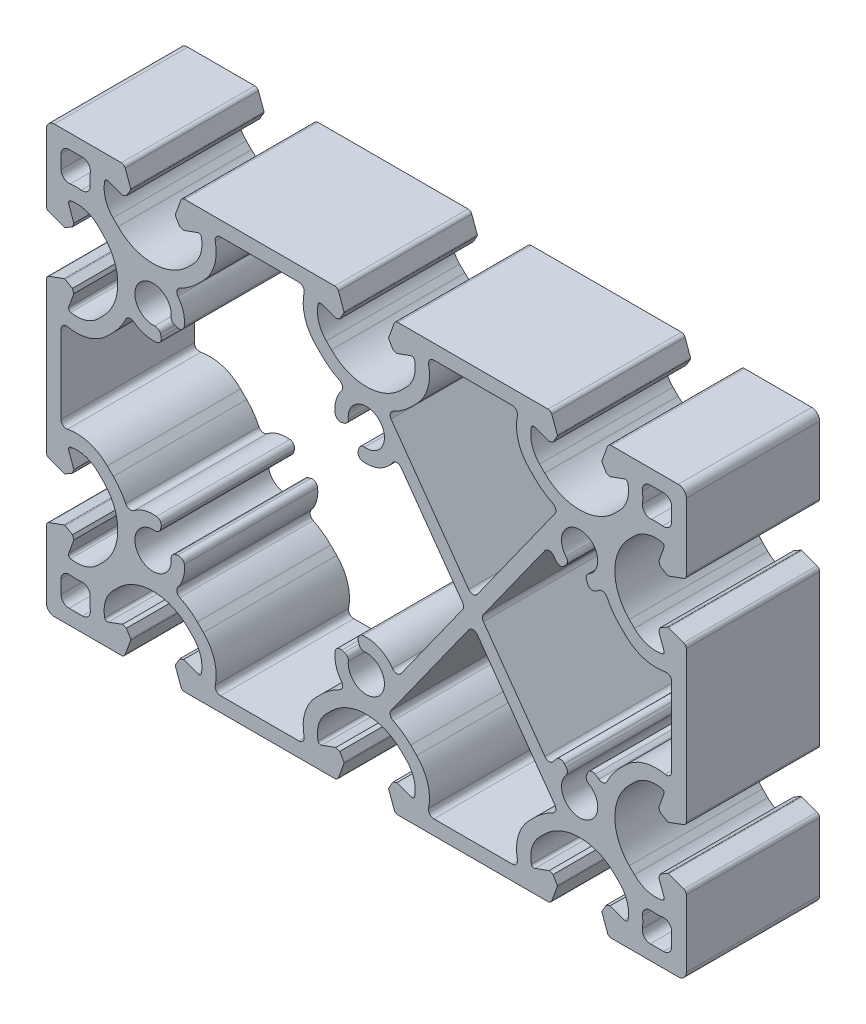
SolidWorks part; units mm, degrees
material "6005-T5"
ref_plane "Front" through (0, 0, 0) normal (0, 0, 1) x (1, 0, 0)
ref_plane "Top" through (0, 0, 0) normal (0, 1, 0) x (1, 0, 0)
ref_plane "Right" through (0, 0, 0) normal (1, 0, 0) x (0, 0, -1)
sketch "Sk Main Extrusion" plane through (0, 0, 0) normal (0, 0, 1) x (1, 0, 0)
  line L0 (-57.25, 35.75) -> (-57.25, 33.2481)
  line L5 (-53.2481, 37.25) -> (-55.75, 37.25)
  line L6 (-38.614, 15.8789) -> (-38.4829, 15.3899)
  line L7 (-47.4415, 11.6915) -> (-48.5773, 10.5557)
  line L8 (-57.25, 7.347) -> (-57.25, -7.347)
  line L9 (-48.5773, -10.5557) -> (-47.4415, -11.6915)
  line L10 (-38.4829, -15.3899) -> (-38.614, -15.8789)
  line L11 (-35.8789, -18.614) -> (-35.3899, -18.4829)
  line L12 (-31.6915, -27.4415) -> (-30.5557, -28.5773)
  line L13 (-27.347, -37.25) -> (-12.653, -37.25)
  line L14 (-9.4443, -28.5773) -> (-8.3085, -27.4415)
  line L15 (-4.6101, -18.4829) -> (-4.1211, -18.614)
  line L16 (-1.386, -15.8789) -> (-1.5171, -15.3899)
  line L17 (6.5268, -16.712) -> (18.0488, -0.5812)
  line L18 (18.0488, 0.5812) -> (6.5268, 16.712)
  line L19 (-1.5171, 15.3899) -> (-1.386, 15.8789)
  line L20 (-4.1211, 18.614) -> (-4.6101, 18.4829)
  line L21 (-8.3085, 27.4415) -> (-9.4443, 28.5773)
  line L22 (-12.653, 37.25) -> (-27.347, 37.25)
  line L23 (-30.5557, 28.5773) -> (-31.6915, 27.4415)
  line L24 (-35.3899, 18.4829) -> (-35.8789, 18.614)
  line L25 (20.8137, 3.2896) -> (35.3545, 23.6466)
  line L26 (31.6915, 27.4415) -> (30.5557, 28.5773)
  line L27 (27.347, 37.25) -> (12.653, 37.25)
  line L28 (9.4443, 28.5773) -> (8.3085, 27.4415)
  line L29 (4.6455, 23.6466) -> (19.1863, 3.2896)
  line L30 (-57.25, -33.2481) -> (-57.25, -35.75)
  line L31 (-55.75, -37.25) -> (-53.2481, -37.25)
  line L32 (19.1863, -3.2896) -> (4.6455, -23.6466)
  line L33 (8.3085, -27.4415) -> (9.4443, -28.5773)
  line L34 (12.653, -37.25) -> (27.347, -37.25)
  line L35 (30.5557, -28.5773) -> (31.6915, -27.4415)
  line L36 (35.3545, -23.6466) -> (20.8137, -3.2896)
  line L37 (41.2964, -15.8498) -> (41.4773, -15.377)
  line L38 (47.4415, -11.6915) -> (48.5773, -10.5557)
  line L39 (57.25, -7.347) -> (57.25, 7.347)
  line L40 (48.5773, 10.5557) -> (47.4415, 11.6915)
  line L41 (41.4773, 15.377) -> (41.2964, 15.8498)
  line L42 (37.4767, 16.4592) -> (37.1577, 16.0661)
  line L43 (33.4732, 16.712) -> (21.9512, 0.5812)
  line L44 (21.9512, -0.5812) -> (33.4732, -16.712)
  line L45 (37.1577, -16.0661) -> (37.4767, -16.4592)
  line L46 (53.2481, -37.25) -> (55.75, -37.25)
  line L47 (57.25, -35.75) -> (57.25, -33.2481)
  line L48 (57.25, 33.2481) -> (57.25, 35.75)
  line L49 (55.75, 37.25) -> (53.2481, 37.25)
  line L50 (-35.8099, -36.6712) -> (-34.7779, -39.5065)
  line L51 (-34.0732, -40) -> (-5.9268, -40)
  line L52 (-5.2221, -39.5065) -> (-4.1901, -36.6712)
  line L53 (-4.2085, -36.4607) -> (-4.9876, -35.1113)
  line L54 (-4.9876, -35.1113) -> (-5.7185, -34.8453)
  line L55 (-5.7185, -34.8453) -> (-8.3962, -35.8198)
  line L56 (-7.5042, -30.2727) -> (-6.5407, -29.3093)
  line L57 (6.5407, -29.3093) -> (7.5042, -30.2727)
  line L58 (8.3962, -35.8198) -> (5.7185, -34.8453)
  line L59 (5.7185, -34.8453) -> (4.9876, -35.1113)
  line L60 (4.9876, -35.1113) -> (4.2085, -36.4607)
  line L61 (4.1901, -36.6712) -> (5.2221, -39.5065)
  line L62 (5.9268, -40) -> (34.0732, -40)
  line L63 (34.7779, -39.5065) -> (35.8099, -36.6712)
  line L64 (35.7915, -36.4607) -> (35.0124, -35.1113)
  line L65 (35.0124, -35.1113) -> (34.2815, -34.8453)
  line L66 (34.2815, -34.8453) -> (31.6038, -35.8198)
  line L67 (32.4958, -30.2727) -> (33.4593, -29.3093)
  line L68 (46.5407, -29.3093) -> (47.5042, -30.2727)
  line L69 (48.3962, -35.8198) -> (45.7185, -34.8453)
  line L70 (45.7185, -34.8453) -> (44.9876, -35.1113)
  line L71 (44.9876, -35.1113) -> (44.2085, -36.4607)
  line L72 (44.1901, -36.6712) -> (45.2221, -39.5065)
  line L73 (45.9268, -40) -> (58.5, -40)
  line L74 (60, -38.5) -> (60, -25.9268)
  line L75 (59.5065, -25.2221) -> (56.6712, -24.1901)
  line L76 (56.4607, -24.2085) -> (55.1113, -24.9876)
  line L77 (55.1113, -24.9876) -> (54.8453, -25.7185)
  line L78 (54.8453, -25.7185) -> (55.8198, -28.3962)
  line L79 (50.2727, -27.5042) -> (49.3093, -26.5407)
  line L80 (49.3093, -13.4593) -> (50.2727, -12.4958)
  line L81 (55.8198, -11.6038) -> (54.8453, -14.2815)
  line L82 (54.8453, -14.2815) -> (55.1113, -15.0124)
  line L83 (55.1113, -15.0124) -> (56.4607, -15.7915)
  line L84 (56.6712, -15.8099) -> (59.5065, -14.7779)
  line L85 (60, -14.0732) -> (60, 14.0732)
  line L86 (59.5065, 14.7779) -> (56.6712, 15.8099)
  line L87 (56.4607, 15.7915) -> (55.1113, 15.0124)
  line L88 (55.1113, 15.0124) -> (54.8453, 14.2815)
  line L89 (54.8453, 14.2815) -> (55.8198, 11.6038)
  line L90 (50.2727, 12.4958) -> (49.3093, 13.4593)
  line L91 (49.3093, 26.5407) -> (50.2727, 27.5042)
  line L92 (55.8198, 28.3962) -> (54.8453, 25.7185)
  line L93 (54.8453, 25.7185) -> (55.1113, 24.9876)
  line L94 (55.1113, 24.9876) -> (56.4607, 24.2085)
  line L95 (56.6712, 24.1901) -> (59.5065, 25.2221)
  line L96 (60, 25.9268) -> (60, 38.5)
  line L97 (58.5, 40) -> (45.9268, 40)
  line L98 (45.2221, 39.5065) -> (44.1901, 36.6712)
  line L99 (44.2085, 36.4607) -> (44.9876, 35.1113)
  line L100 (44.9876, 35.1113) -> (45.7185, 34.8453)
  line L101 (45.7185, 34.8453) -> (48.3962, 35.8198)
  line L102 (47.5042, 30.2727) -> (46.5407, 29.3093)
  line L103 (33.4593, 29.3093) -> (32.4958, 30.2727)
  line L104 (31.6038, 35.8198) -> (34.2815, 34.8453)
  line L105 (34.2815, 34.8453) -> (35.0124, 35.1113)
  line L106 (35.0124, 35.1113) -> (35.7915, 36.4607)
  line L107 (35.8099, 36.6712) -> (34.7779, 39.5065)
  line L108 (34.0732, 40) -> (5.9268, 40)
  line L109 (5.2221, 39.5065) -> (4.1901, 36.6712)
  line L110 (4.2085, 36.4607) -> (4.9876, 35.1113)
  line L111 (4.9876, 35.1113) -> (5.7185, 34.8453)
  line L112 (5.7185, 34.8453) -> (8.3962, 35.8198)
  line L113 (7.5042, 30.2727) -> (6.5407, 29.3093)
  line L114 (-6.5407, 29.3093) -> (-7.5042, 30.2727)
  line L115 (-8.3962, 35.8198) -> (-5.7185, 34.8453)
  line L116 (-5.7185, 34.8453) -> (-4.9876, 35.1113)
  line L117 (-4.9876, 35.1113) -> (-4.2085, 36.4607)
  line L118 (-4.1901, 36.6712) -> (-5.2221, 39.5065)
  line L119 (-5.9268, 40) -> (-34.0732, 40)
  line L120 (-34.7779, 39.5065) -> (-35.8099, 36.6712)
  line L121 (-35.7915, 36.4607) -> (-35.0124, 35.1113)
  line L122 (-35.0124, 35.1113) -> (-34.2815, 34.8453)
  line L123 (-34.2815, 34.8453) -> (-31.6038, 35.8198)
  line L124 (-32.4958, 30.2727) -> (-33.4593, 29.3093)
  line L125 (-46.5407, 29.3093) -> (-47.5042, 30.2727)
  line L126 (-48.3962, 35.8198) -> (-45.7185, 34.8453)
  line L127 (-45.7185, 34.8453) -> (-44.9876, 35.1113)
  line L128 (-44.9876, 35.1113) -> (-44.2085, 36.4607)
  line L129 (-44.1901, 36.6712) -> (-45.2221, 39.5065)
  line L130 (-45.9268, 40) -> (-58.5, 40)
  line L131 (-60, 38.5) -> (-60, 25.9268)
  line L132 (-59.5065, 25.2221) -> (-56.6712, 24.1901)
  line L133 (-56.4607, 24.2085) -> (-55.1113, 24.9876)
  line L134 (-55.1113, 24.9876) -> (-54.8453, 25.7185)
  line L135 (-54.8453, 25.7185) -> (-55.8198, 28.3962)
  line L136 (-50.2727, 27.5042) -> (-49.3093, 26.5407)
  line L137 (-49.3093, 13.4593) -> (-50.2727, 12.4958)
  line L138 (-55.8198, 11.6038) -> (-54.8453, 14.2815)
  line L139 (-54.8453, 14.2815) -> (-55.1113, 15.0124)
  line L140 (-55.1113, 15.0124) -> (-56.4607, 15.7915)
  line L141 (-56.6712, 15.8099) -> (-59.5065, 14.7779)
  line L142 (-60, 14.0732) -> (-60, -14.0732)
  line L143 (-59.5065, -14.7779) -> (-56.6712, -15.8099)
  line L144 (-56.4607, -15.7915) -> (-55.1113, -15.0124)
  line L145 (-55.1113, -15.0124) -> (-54.8453, -14.2815)
  line L146 (-54.8453, -14.2815) -> (-55.8198, -11.6038)
  line L147 (-50.2727, -12.4958) -> (-49.3093, -13.4593)
  line L148 (-49.3093, -26.5407) -> (-50.2727, -27.5042)
  line L149 (-55.8198, -28.3962) -> (-54.8453, -25.7185)
  line L150 (-54.8453, -25.7185) -> (-55.1113, -24.9876)
  line L151 (-55.1113, -24.9876) -> (-56.4607, -24.2085)
  line L152 (-56.6712, -24.1901) -> (-59.5065, -25.2221)
  line L153 (-60, -25.9268) -> (-60, -38.5)
  line L154 (-58.5, -40) -> (-45.9268, -40)
  line L155 (-45.2221, -39.5065) -> (-44.1901, -36.6712)
  line L156 (-44.2085, -36.4607) -> (-44.9876, -35.1113)
  line L157 (-44.9876, -35.1113) -> (-45.7185, -34.8453)
  line L158 (-45.7185, -34.8453) -> (-48.3962, -35.8198)
  line L159 (-47.5042, -30.2727) -> (-46.5407, -29.3093)
  line L160 (-33.4593, -29.3093) -> (-32.4958, -30.2727)
  line L161 (-31.6038, -35.8198) -> (-34.2815, -34.8453)
  line L162 (-34.2815, -34.8453) -> (-35.0124, -35.1113)
  line L163 (-35.0124, -35.1113) -> (-35.7915, -36.4607)
  line L164 (-57.25, 0) -> (57.25, 0) construction
  line L165 (0, 0) -> (0, 40) construction
  arc A0 (-55.75, 37.25) -> (-57.25, 35.75) centre (-55.75, 35.75) ccw
  arc A1 (-57.25, 33.2481) -> (-55.5375, 31.7633) centre (-55.75, 33.2481) ccw
  arc A2 (-53.4532, 31.794) -> (-55.5375, 31.7633) centre (-54.3755, 23.646) ccw
  arc A3 (-53.4532, 31.794) -> (-51.794, 33.4532) centre (-53.2844, 33.2844) ccw
  arc A4 (-51.7633, 35.5375) -> (-51.794, 33.4532) centre (-43.646, 34.3755) ccw
  arc A5 (-51.7633, 35.5375) -> (-53.2481, 37.25) centre (-53.2481, 35.75) ccw
  arc A6 (-38.614, 15.8789) -> (-39.6754, 16.6155) centre (-39.5799, 15.6201) ccw
  arc A7 (-39.3364, 14.1374) -> (-38.4829, 15.3899) centre (-39.4489, 15.1311) ccw
  arc A8 (-43.6133, 15.3359) -> (-39.3364, 14.1374) centre (-40, 20) ccw
  arc A9 (-43.6133, 15.3359) -> (-45.1296, 14.9732) centre (-44.2257, 14.5453) ccw
  arc A10 (-47.4415, 11.6915) -> (-45.1296, 14.9732) centre (-55.75, 20) ccw
  arc A11 (-56.0463, 8.326) -> (-48.5773, 10.5557) centre (-54.3755, 16.354) ccw
  arc A12 (-56.0463, 8.326) -> (-57.25, 7.347) centre (-56.25, 7.347) ccw
  arc A13 (-57.25, -7.347) -> (-56.0463, -8.326) centre (-56.25, -7.347) ccw
  arc A14 (-48.5773, -10.5557) -> (-56.0463, -8.326) centre (-54.3755, -16.354) ccw
  arc A15 (-45.1296, -14.9732) -> (-47.4415, -11.6915) centre (-55.75, -20) ccw
  arc A16 (-45.1296, -14.9732) -> (-43.6133, -15.3359) centre (-44.2257, -14.5453) ccw
  arc A17 (-39.3364, -14.1374) -> (-43.6133, -15.3359) centre (-40, -20) ccw
  arc A18 (-38.4829, -15.3899) -> (-39.3364, -14.1374) centre (-39.4489, -15.1311) ccw
  arc A19 (-39.6754, -16.6155) -> (-38.614, -15.8789) centre (-39.5799, -15.6201) ccw
  arc A20 (-39.6754, -16.6155) -> (-36.6155, -19.6754) centre (-40, -20) ccw
  arc A21 (-35.8789, -18.614) -> (-36.6155, -19.6754) centre (-35.6201, -19.5799) ccw
  arc A22 (-34.1374, -19.3364) -> (-35.3899, -18.4829) centre (-35.1311, -19.4489) ccw
  arc A23 (-35.3359, -23.6133) -> (-34.1374, -19.3364) centre (-40, -20) ccw
  arc A24 (-35.3359, -23.6133) -> (-34.9732, -25.1296) centre (-34.5453, -24.2257) ccw
  arc A25 (-31.6915, -27.4415) -> (-34.9732, -25.1296) centre (-40, -35.75) ccw
  arc A26 (-28.326, -36.0463) -> (-30.5557, -28.5773) centre (-36.354, -34.3755) ccw
  arc A27 (-28.326, -36.0463) -> (-27.347, -37.25) centre (-27.347, -36.25) ccw
  arc A28 (-12.653, -37.25) -> (-11.674, -36.0463) centre (-12.653, -36.25) ccw
  arc A29 (-9.4443, -28.5773) -> (-11.674, -36.0463) centre (-3.646, -34.3755) ccw
  arc A30 (-5.0268, -25.1296) -> (-8.3085, -27.4415) centre (0, -35.75) ccw
  arc A31 (-5.0268, -25.1296) -> (-4.6641, -23.6133) centre (-5.4547, -24.2257) ccw
  arc A32 (-5.8626, -19.3364) -> (-4.6641, -23.6133) centre (0, -20) ccw
  arc A33 (-34.7779, -39.5065) -> (-34.0732, -40) centre (-34.0732, -39.25) ccw
  arc A34 (-5.9268, -40) -> (-5.2221, -39.5065) centre (-5.9268, -39.25) ccw
  arc A35 (-4.1901, -36.6712) -> (-4.2085, -36.4607) centre (-4.425, -36.5857) ccw
  arc A36 (-9.057, -35.4507) -> (-8.3962, -35.8198) centre (-8.5672, -35.35) ccw
  arc A37 (-7.5042, -30.2727) -> (-9.057, -35.4507) centre (-3.4737, -34.3032) ccw
  arc A38 (6.5407, -29.3093) -> (-6.5407, -29.3093) centre (0, -35.85) ccw
  arc A39 (9.057, -35.4507) -> (7.5042, -30.2727) centre (3.4737, -34.3032) ccw
  arc A40 (8.3962, -35.8198) -> (9.057, -35.4507) centre (8.5672, -35.35) ccw
  arc A41 (4.2085, -36.4607) -> (4.1901, -36.6712) centre (4.425, -36.5857) ccw
  arc A42 (5.2221, -39.5065) -> (5.9268, -40) centre (5.9268, -39.25) ccw
  arc A43 (34.0732, -40) -> (34.7779, -39.5065) centre (34.0732, -39.25) ccw
  arc A44 (35.8099, -36.6712) -> (35.7915, -36.4607) centre (35.575, -36.5857) ccw
  arc A45 (30.943, -35.4507) -> (31.6038, -35.8198) centre (31.4328, -35.35) ccw
  arc A46 (32.4958, -30.2727) -> (30.943, -35.4507) centre (36.5263, -34.3032) ccw
  arc A47 (46.5407, -29.3093) -> (33.4593, -29.3093) centre (40, -35.85) ccw
  arc A48 (49.057, -35.4507) -> (47.5042, -30.2727) centre (43.4737, -34.3032) ccw
  arc A49 (48.3962, -35.8198) -> (49.057, -35.4507) centre (48.5672, -35.35) ccw
  arc A50 (44.2085, -36.4607) -> (44.1901, -36.6712) centre (44.425, -36.5857) ccw
  arc A51 (45.2221, -39.5065) -> (45.9268, -40) centre (45.9268, -39.25) ccw
  arc A52 (58.5, -40) -> (60, -38.5) centre (58.5, -38.5) ccw
  arc A53 (60, -25.9268) -> (59.5065, -25.2221) centre (59.25, -25.9268) ccw
  arc A54 (56.6712, -24.1901) -> (56.4607, -24.2085) centre (56.5857, -24.425) ccw
  arc A55 (55.4507, -29.057) -> (55.8198, -28.3962) centre (55.35, -28.5672) ccw
  arc A56 (50.2727, -27.5042) -> (55.4507, -29.057) centre (54.3032, -23.4737) ccw
  arc A57 (49.3093, -13.4593) -> (49.3093, -26.5407) centre (55.85, -20) ccw
  arc A58 (55.4507, -10.943) -> (50.2727, -12.4958) centre (54.3032, -16.5263) ccw
  arc A59 (55.8198, -11.6038) -> (55.4507, -10.943) centre (55.35, -11.4328) ccw
  arc A60 (56.4607, -15.7915) -> (56.6712, -15.8099) centre (56.5857, -15.575) ccw
  arc A61 (59.5065, -14.7779) -> (60, -14.0732) centre (59.25, -14.0732) ccw
  arc A62 (60, 14.0732) -> (59.5065, 14.7779) centre (59.25, 14.0732) ccw
  arc A63 (56.6712, 15.8099) -> (56.4607, 15.7915) centre (56.5857, 15.575) ccw
  arc A64 (55.4507, 10.943) -> (55.8198, 11.6038) centre (55.35, 11.4328) ccw
  arc A65 (50.2727, 12.4958) -> (55.4507, 10.943) centre (54.3032, 16.5263) ccw
  arc A66 (49.3093, 26.5407) -> (49.3093, 13.4593) centre (55.85, 20) ccw
  arc A67 (55.4507, 29.057) -> (50.2727, 27.5042) centre (54.3032, 23.4737) ccw
  arc A68 (55.8198, 28.3962) -> (55.4507, 29.057) centre (55.35, 28.5672) ccw
  arc A69 (56.4607, 24.2085) -> (56.6712, 24.1901) centre (56.5857, 24.425) ccw
  arc A70 (59.5065, 25.2221) -> (60, 25.9268) centre (59.25, 25.9268) ccw
  arc A71 (60, 38.5) -> (58.5, 40) centre (58.5, 38.5) ccw
  arc A72 (45.9268, 40) -> (45.2221, 39.5065) centre (45.9268, 39.25) ccw
  arc A73 (44.1901, 36.6712) -> (44.2085, 36.4607) centre (44.425, 36.5857) ccw
  arc A74 (49.057, 35.4507) -> (48.3962, 35.8198) centre (48.5672, 35.35) ccw
  arc A75 (47.5042, 30.2727) -> (49.057, 35.4507) centre (43.4737, 34.3032) ccw
  arc A76 (33.4593, 29.3093) -> (46.5407, 29.3093) centre (40, 35.85) ccw
  arc A77 (30.943, 35.4507) -> (32.4958, 30.2727) centre (36.5263, 34.3032) ccw
  arc A78 (31.6038, 35.8198) -> (30.943, 35.4507) centre (31.4328, 35.35) ccw
  arc A79 (35.7915, 36.4607) -> (35.8099, 36.6712) centre (35.575, 36.5857) ccw
  arc A80 (34.7779, 39.5065) -> (34.0732, 40) centre (34.0732, 39.25) ccw
  arc A81 (5.9268, 40) -> (5.2221, 39.5065) centre (5.9268, 39.25) ccw
  arc A82 (4.1901, 36.6712) -> (4.2085, 36.4607) centre (4.425, 36.5857) ccw
  arc A83 (9.057, 35.4507) -> (8.3962, 35.8198) centre (8.5672, 35.35) ccw
  arc A84 (7.5042, 30.2727) -> (9.057, 35.4507) centre (3.4737, 34.3032) ccw
  arc A85 (-6.5407, 29.3093) -> (6.5407, 29.3093) centre (0, 35.85) ccw
  arc A86 (-9.057, 35.4507) -> (-7.5042, 30.2727) centre (-3.4737, 34.3032) ccw
  arc A87 (-8.3962, 35.8198) -> (-9.057, 35.4507) centre (-8.5672, 35.35) ccw
  arc A88 (-4.2085, 36.4607) -> (-4.1901, 36.6712) centre (-4.425, 36.5857) ccw
  arc A89 (-5.2221, 39.5065) -> (-5.9268, 40) centre (-5.9268, 39.25) ccw
  arc A90 (-34.0732, 40) -> (-34.7779, 39.5065) centre (-34.0732, 39.25) ccw
  arc A91 (-35.8099, 36.6712) -> (-35.7915, 36.4607) centre (-35.575, 36.5857) ccw
  arc A92 (-30.943, 35.4507) -> (-31.6038, 35.8198) centre (-31.4328, 35.35) ccw
  arc A93 (-32.4958, 30.2727) -> (-30.943, 35.4507) centre (-36.5263, 34.3032) ccw
  arc A94 (-46.5407, 29.3093) -> (-33.4593, 29.3093) centre (-40, 35.85) ccw
  arc A95 (-49.057, 35.4507) -> (-47.5042, 30.2727) centre (-43.4737, 34.3032) ccw
  arc A96 (-48.3962, 35.8198) -> (-49.057, 35.4507) centre (-48.5672, 35.35) ccw
  arc A97 (-44.2085, 36.4607) -> (-44.1901, 36.6712) centre (-44.425, 36.5857) ccw
  arc A98 (-45.2221, 39.5065) -> (-45.9268, 40) centre (-45.9268, 39.25) ccw
  arc A99 (-58.5, 40) -> (-60, 38.5) centre (-58.5, 38.5) ccw
  arc A100 (-60, 25.9268) -> (-59.5065, 25.2221) centre (-59.25, 25.9268) ccw
  arc A101 (-56.6712, 24.1901) -> (-56.4607, 24.2085) centre (-56.5857, 24.425) ccw
  arc A102 (-55.4507, 29.057) -> (-55.8198, 28.3962) centre (-55.35, 28.5672) ccw
  arc A103 (-50.2727, 27.5042) -> (-55.4507, 29.057) centre (-54.3032, 23.4737) ccw
  arc A104 (-49.3093, 13.4593) -> (-49.3093, 26.5407) centre (-55.85, 20) ccw
  arc A105 (-55.4507, 10.943) -> (-50.2727, 12.4958) centre (-54.3032, 16.5263) ccw
  arc A106 (-55.8198, 11.6038) -> (-55.4507, 10.943) centre (-55.35, 11.4328) ccw
  arc A107 (-56.4607, 15.7915) -> (-56.6712, 15.8099) centre (-56.5857, 15.575) ccw
  arc A108 (-59.5065, 14.7779) -> (-60, 14.0732) centre (-59.25, 14.0732) ccw
  arc A109 (-60, -14.0732) -> (-59.5065, -14.7779) centre (-59.25, -14.0732) ccw
  arc A110 (-56.6712, -15.8099) -> (-56.4607, -15.7915) centre (-56.5857, -15.575) ccw
  arc A111 (-55.4507, -10.943) -> (-55.8198, -11.6038) centre (-55.35, -11.4328) ccw
  arc A112 (-50.2727, -12.4958) -> (-55.4507, -10.943) centre (-54.3032, -16.5263) ccw
  arc A113 (-49.3093, -26.5407) -> (-49.3093, -13.4593) centre (-55.85, -20) ccw
  arc A114 (-55.4507, -29.057) -> (-50.2727, -27.5042) centre (-54.3032, -23.4737) ccw
  arc A115 (-55.8198, -28.3962) -> (-55.4507, -29.057) centre (-55.35, -28.5672) ccw
  arc A116 (-56.4607, -24.2085) -> (-56.6712, -24.1901) centre (-56.5857, -24.425) ccw
  arc A117 (-59.5065, -25.2221) -> (-60, -25.9268) centre (-59.25, -25.9268) ccw
  arc A118 (-60, -38.5) -> (-58.5, -40) centre (-58.5, -38.5) ccw
  arc A119 (-45.9268, -40) -> (-45.2221, -39.5065) centre (-45.9268, -39.25) ccw
  arc A120 (-44.1901, -36.6712) -> (-44.2085, -36.4607) centre (-44.425, -36.5857) ccw
  arc A121 (-49.057, -35.4507) -> (-48.3962, -35.8198) centre (-48.5672, -35.35) ccw
  arc A122 (-47.5042, -30.2727) -> (-49.057, -35.4507) centre (-43.4737, -34.3032) ccw
  arc A123 (-33.4593, -29.3093) -> (-46.5407, -29.3093) centre (-40, -35.85) ccw
  arc A124 (-30.943, -35.4507) -> (-32.4958, -30.2727) centre (-36.5263, -34.3032) ccw
  arc A125 (-31.6038, -35.8198) -> (-30.943, -35.4507) centre (-31.4328, -35.35) ccw
  arc A126 (-35.7915, -36.4607) -> (-35.8099, -36.6712) centre (-35.575, -36.5857) ccw
  arc A127 (-4.6101, -18.4829) -> (-5.8626, -19.3364) centre (-4.8689, -19.4489) ccw
  arc A128 (-3.3845, -19.6754) -> (-4.1211, -18.614) centre (-4.3799, -19.5799) ccw
  arc A129 (-3.3845, -19.6754) -> (-0.3246, -16.6155) centre (0, -20) ccw
  arc A130 (-1.386, -15.8789) -> (-0.3246, -16.6155) centre (-0.4201, -15.6201) ccw
  arc A131 (-0.6636, -14.1374) -> (-1.5171, -15.3899) centre (-0.5511, -15.1311) ccw
  arc A132 (4.8851, -16.6916) -> (-0.6636, -14.1374) centre (0, -20) ccw
  arc A133 (4.8851, -16.6916) -> (6.5268, -16.712) centre (5.7131, -16.1308) ccw
  arc A134 (18.0488, -0.5812) -> (18.0488, 0.5812) centre (17.2351, 0) ccw
  arc A135 (6.5268, 16.712) -> (4.8851, 16.6916) centre (5.7131, 16.1308) ccw
  arc A136 (-0.6636, 14.1374) -> (4.8851, 16.6916) centre (0, 20) ccw
  arc A137 (-1.5171, 15.3899) -> (-0.6636, 14.1374) centre (-0.5511, 15.1311) ccw
  arc A138 (-0.3246, 16.6155) -> (-1.386, 15.8789) centre (-0.4201, 15.6201) ccw
  arc A139 (-0.3246, 16.6155) -> (-3.3845, 19.6754) centre (0, 20) ccw
  arc A140 (-4.1211, 18.614) -> (-3.3845, 19.6754) centre (-4.3799, 19.5799) ccw
  arc A141 (-5.8626, 19.3364) -> (-4.6101, 18.4829) centre (-4.8689, 19.4489) ccw
  arc A142 (-4.6641, 23.6133) -> (-5.8626, 19.3364) centre (0, 20) ccw
  arc A143 (-4.6641, 23.6133) -> (-5.0268, 25.1296) centre (-5.4547, 24.2257) ccw
  arc A144 (-8.3085, 27.4415) -> (-5.0268, 25.1296) centre (0, 35.75) ccw
  arc A145 (-11.674, 36.0463) -> (-9.4443, 28.5773) centre (-3.646, 34.3755) ccw
  arc A146 (-11.674, 36.0463) -> (-12.653, 37.25) centre (-12.653, 36.25) ccw
  arc A147 (-27.347, 37.25) -> (-28.326, 36.0463) centre (-27.347, 36.25) ccw
  arc A148 (-30.5557, 28.5773) -> (-28.326, 36.0463) centre (-36.354, 34.3755) ccw
  arc A149 (-34.9732, 25.1296) -> (-31.6915, 27.4415) centre (-40, 35.75) ccw
  arc A150 (-34.9732, 25.1296) -> (-35.3359, 23.6133) centre (-34.5453, 24.2257) ccw
  arc A151 (-34.1374, 19.3364) -> (-35.3359, 23.6133) centre (-40, 20) ccw
  arc A152 (-35.3899, 18.4829) -> (-34.1374, 19.3364) centre (-35.1311, 19.4489) ccw
  arc A153 (-36.6155, 19.6754) -> (-35.8789, 18.614) centre (-35.6201, 19.5799) ccw
  arc A154 (-36.6155, 19.6754) -> (-39.6754, 16.6155) centre (-40, 20) ccw
  arc A155 (19.1863, 3.2896) -> (20.8137, 3.2896) centre (20, 3.8708) ccw
  arc A156 (35.3545, 23.6466) -> (34.9689, 25.1316) centre (34.5408, 24.2279) ccw
  arc A157 (31.6915, 27.4415) -> (34.9689, 25.1316) centre (40, 35.75) ccw
  arc A158 (28.326, 36.0463) -> (30.5557, 28.5773) centre (36.354, 34.3755) ccw
  arc A159 (28.326, 36.0463) -> (27.347, 37.25) centre (27.347, 36.25) ccw
  arc A160 (12.653, 37.25) -> (11.674, 36.0463) centre (12.653, 36.25) ccw
  arc A161 (9.4443, 28.5773) -> (11.674, 36.0463) centre (3.646, 34.3755) ccw
  arc A162 (5.0311, 25.1316) -> (8.3085, 27.4415) centre (0, 35.75) ccw
  arc A163 (5.0311, 25.1316) -> (4.6455, 23.6466) centre (5.4592, 24.2279) ccw
  arc A164 (-55.5375, -31.7633) -> (-57.25, -33.2481) centre (-55.75, -33.2481) ccw
  arc A165 (-57.25, -35.75) -> (-55.75, -37.25) centre (-55.75, -35.75) ccw
  arc A166 (-53.2481, -37.25) -> (-51.7633, -35.5375) centre (-53.2481, -35.75) ccw
  arc A167 (-51.794, -33.4532) -> (-51.7633, -35.5375) centre (-43.646, -34.3755) ccw
  arc A168 (-51.794, -33.4532) -> (-53.4532, -31.794) centre (-53.2844, -33.2844) ccw
  arc A169 (-55.5375, -31.7633) -> (-53.4532, -31.794) centre (-54.3755, -23.646) ccw
  arc A170 (20.8137, -3.2896) -> (19.1863, -3.2896) centre (20, -3.8708) ccw
  arc A171 (4.6455, -23.6466) -> (5.0311, -25.1316) centre (5.4592, -24.2279) ccw
  arc A172 (8.3085, -27.4415) -> (5.0311, -25.1316) centre (0, -35.75) ccw
  arc A173 (11.674, -36.0463) -> (9.4443, -28.5773) centre (3.646, -34.3755) ccw
  arc A174 (11.674, -36.0463) -> (12.653, -37.25) centre (12.653, -36.25) ccw
  arc A175 (27.347, -37.25) -> (28.326, -36.0463) centre (27.347, -36.25) ccw
  arc A176 (30.5557, -28.5773) -> (28.326, -36.0463) centre (36.354, -34.3755) ccw
  arc A177 (34.9689, -25.1316) -> (31.6915, -27.4415) centre (40, -35.75) ccw
  arc A178 (34.9689, -25.1316) -> (35.3545, -23.6466) centre (34.5408, -24.2279) ccw
  arc A179 (41.2964, -15.8498) -> (41.7235, -17.0692) centre (42.2304, -16.2072) ccw
  arc A180 (42.9034, -14.8638) -> (41.4773, -15.377) centre (42.4113, -15.7343) ccw
  arc A181 (43.6133, -15.3359) -> (42.9034, -14.8638) centre (40, -20) ccw
  arc A182 (43.6133, -15.3359) -> (45.1296, -14.9732) centre (44.2257, -14.5453) ccw
  arc A183 (47.4415, -11.6915) -> (45.1296, -14.9732) centre (55.75, -20) ccw
  arc A184 (56.0463, -8.326) -> (48.5773, -10.5557) centre (54.3755, -16.354) ccw
  arc A185 (56.0463, -8.326) -> (57.25, -7.347) centre (56.25, -7.347) ccw
  arc A186 (57.25, 7.347) -> (56.0463, 8.326) centre (56.25, 7.347) ccw
  arc A187 (48.5773, 10.5557) -> (56.0463, 8.326) centre (54.3755, 16.354) ccw
  arc A188 (45.1296, 14.9732) -> (47.4415, 11.6915) centre (55.75, 20) ccw
  arc A189 (45.1296, 14.9732) -> (43.6133, 15.3359) centre (44.2257, 14.5453) ccw
  arc A190 (42.9034, 14.8638) -> (43.6133, 15.3359) centre (40, 20) ccw
  arc A191 (41.4773, 15.377) -> (42.9034, 14.8638) centre (42.4113, 15.7343) ccw
  arc A192 (41.7235, 17.0692) -> (41.2964, 15.8498) centre (42.2304, 16.2072) ccw
  arc A193 (41.7235, 17.0692) -> (37.4502, 17.7509) centre (40, 20) ccw
  arc A194 (37.4767, 16.4592) -> (37.4502, 17.7509) centre (36.7003, 17.0894) ccw
  arc A195 (35.6427, 16.022) -> (37.1577, 16.0661) centre (36.3812, 16.6963) ccw
  arc A196 (35.1149, 16.6916) -> (35.6427, 16.022) centre (40, 20) ccw
  arc A197 (35.1149, 16.6916) -> (33.4732, 16.712) centre (34.2869, 16.1308) ccw
  arc A198 (21.9512, 0.5812) -> (21.9512, -0.5812) centre (22.7649, 0) ccw
  arc A199 (33.4732, -16.712) -> (35.1149, -16.6916) centre (34.2869, -16.1308) ccw
  arc A200 (35.6427, -16.022) -> (35.1149, -16.6916) centre (40, -20) ccw
  arc A201 (37.1577, -16.0661) -> (35.6427, -16.022) centre (36.3812, -16.6963) ccw
  arc A202 (37.4502, -17.7509) -> (37.4767, -16.4592) centre (36.7003, -17.0894) ccw
  arc A203 (37.4502, -17.7509) -> (41.7235, -17.0692) centre (40, -20) ccw
  arc A204 (53.4532, -31.794) -> (51.794, -33.4532) centre (53.2844, -33.2844) ccw
  arc A205 (51.7633, -35.5375) -> (51.794, -33.4532) centre (43.646, -34.3755) ccw
  arc A206 (51.7633, -35.5375) -> (53.2481, -37.25) centre (53.2481, -35.75) ccw
  arc A207 (55.75, -37.25) -> (57.25, -35.75) centre (55.75, -35.75) ccw
  arc A208 (57.25, -33.2481) -> (55.5375, -31.7633) centre (55.75, -33.2481) ccw
  arc A209 (53.4532, -31.794) -> (55.5375, -31.7633) centre (54.3755, -23.646) ccw
  arc A210 (55.5375, 31.7633) -> (53.4532, 31.794) centre (54.3755, 23.646) ccw
  arc A211 (55.5375, 31.7633) -> (57.25, 33.2481) centre (55.75, 33.2481) ccw
  arc A212 (57.25, 35.75) -> (55.75, 37.25) centre (55.75, 35.75) ccw
  arc A213 (53.2481, 37.25) -> (51.7633, 35.5375) centre (53.2481, 35.75) ccw
  arc A214 (51.794, 33.4532) -> (51.7633, 35.5375) centre (43.646, 34.3755) ccw
  arc A215 (51.794, 33.4532) -> (53.4532, 31.794) centre (53.2844, 33.2844) ccw
extrude "Main Extrusion" add sketch "Sk Main Extrusion" against normal blind 25
sketch "Threaded Insert Mate Sketch" plane through (0, 0, 0) normal (0, 0, 1) x (1, 0, 0)
  line L0 (-20, 40) -> (-20, -40) construction
  line L1 (-5.9268, 40) -> (-34.0732, 40) construction
  line L2 (-34.0732, -40) -> (-5.9268, -40) construction
  line L3 (-57.25, 0) -> (57.25, 0) construction
  line L4 (-57.25, 7.347) -> (-57.25, -7.347) construction
  line L5 (57.25, -7.347) -> (57.25, 7.347) construction
  line L6 (0, 32.7) -> (0, 0) construction
  circle A0 centre (0, 32.7) radius 5.6515
  arc A1 (-0.3246, 16.6155) -> (-3.3845, 19.6754) centre (0, 20) ccw construction
  circle A2 centre (-40, 32.7) radius 5.6515
  circle A3 centre (40, 32.7) radius 5.6515
  circle A4 centre (40, -32.7) radius 5.6515
  circle A5 centre (0, -32.7) radius 5.6515
  circle A6 centre (-40, -32.7) radius 5.6515
  circle A7 centre (-27.3, 20) radius 5.6515
  circle A8 centre (-40, 7.3) radius 5.6515
  circle A9 centre (-52.7, 20) radius 5.6515
  arc A10 (-36.6155, 19.6754) -> (-39.6754, 16.6155) centre (-40, 20) ccw construction
  circle A11 centre (-52.7, -20) radius 5.6515
  circle A12 centre (52.7, -20) radius 5.6515
  circle A13 centre (52.7, 20) radius 5.6515
  point P29 (0, 0)
  point P38 (-40, 20)
  dimension "D2" = 11.303
  dimension "D1" = 12.7
  dimension "D3" = 4
equation "\"Weight kg\"= round ( \"SW-Mass\" , 2 )"
equation "\"Weight lbs\"= round ( \"SW-Mass\" * 2.2046 , 2 )"
equation "\"Length mm\"= round ( \"Length@Main Extrusion\" , 2 )"
equation "\"Length in\"= round ( \"Length@Main Extrusion\" / 25.4 , 3 )"
